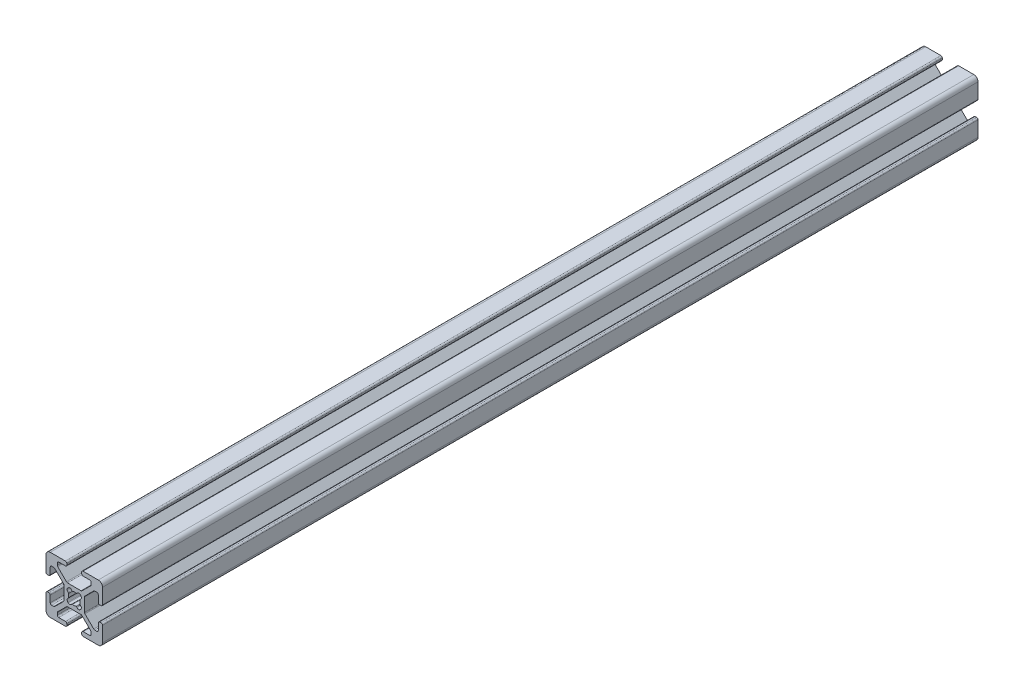
SolidWorks part; units mm, degrees
ref_plane "Front Plane" through (0, 0, 0) normal (0, 0, 1) x (1, 0, 0)
ref_plane "Top Plane" through (0, 0, 0) normal (0, 1, 0) x (1, 0, 0)
ref_plane "Right Plane" through (0, 0, 0) normal (1, 0, 0) x (0, 0, -1)
sketch "Sketch1" plane through (0, 0, 0) normal (1, 0, 0) x (0, 0, -1)
  line L0 (0, 0) -> (310, 0)
  dimension "D1" = 310
other "20_series 20-2020(1)"
ref_plane "Plane1" through (0, 0, 0) normal (0, 0, -1) x (0, 1, 0)
sketch "Sketch11" plane through (0, 0, 0) normal (0, 0, -1) x (0, 1, 0)
  line L0 (9.0094, 2.6289) -> (9.492, 2.6289)
  line L1 (8.5014, 5.4864) -> (8.5014, 3.1369)
  line L2 (10, 8.5014) -> (10, 3.1369)
  line L3 (7.2645, 5.9944) -> (7.9934, 5.9944)
  line L4 (3.1369, 10) -> (8.5014, 10)
  line L5 (3.8074, 2.7477) -> (6.9053, 5.8456)
  line L6 (2.6289, 9.0094) -> (2.6289, 9.492)
  line L7 (3.6586, -2.3885) -> (3.6586, 2.3885)
  line L8 (3.1369, 8.5014) -> (5.4864, 8.5014)
  line L9 (6.9053, -5.8456) -> (3.8074, -2.7477)
  line L10 (5.9944, 7.9934) -> (5.9944, 7.2645)
  line L11 (7.9934, -5.9944) -> (7.2645, -5.9944)
  line L12 (5.8456, 6.9053) -> (2.7477, 3.8074)
  line L13 (8.5014, -3.1369) -> (8.5014, -5.4864)
  line L14 (2.3885, 3.6586) -> (-2.3885, 3.6586)
  line L15 (9.0094, -2.6289) -> (9.492, -2.6289)
  line L16 (-2.7477, 3.8074) -> (-5.8456, 6.9053)
  line L17 (10, -3.1369) -> (10, -8.5014)
  line L18 (-5.9944, 7.2645) -> (-5.9944, 7.9934)
  line L19 (8.5014, -10) -> (3.1369, -10)
  line L20 (-5.4864, 8.5014) -> (-3.1369, 8.5014)
  line L21 (2.6289, -9.0094) -> (2.6289, -9.492)
  line L22 (-2.6289, 9.0094) -> (-2.6289, 9.492)
  line L23 (5.4864, -8.5014) -> (3.1369, -8.5014)
  line L24 (-8.5014, 10) -> (-3.1369, 10)
  line L25 (5.9944, -7.2645) -> (5.9944, -7.9934)
  line L26 (-10, 3.1369) -> (-10, 8.5014)
  line L27 (2.7477, -3.8074) -> (5.8456, -6.9053)
  line L28 (-9.0094, 2.6289) -> (-9.492, 2.6289)
  line L29 (-2.3885, -3.6586) -> (2.3885, -3.6586)
  line L30 (-8.5014, 3.1369) -> (-8.5014, 5.4864)
  line L31 (-5.8456, -6.9053) -> (-2.7477, -3.8074)
  line L32 (-7.9934, 5.9944) -> (-7.2645, 5.9944)
  line L33 (-5.9944, -7.9934) -> (-5.9944, -7.2645)
  line L34 (-6.9053, 5.8456) -> (-3.8074, 2.7477)
  line L35 (-3.1369, -8.5014) -> (-5.4864, -8.5014)
  line L36 (-3.6586, 2.3885) -> (-3.6586, -2.3885)
  line L37 (-2.6289, -9.0094) -> (-2.6289, -9.492)
  line L38 (-3.8074, -2.7477) -> (-6.9053, -5.8456)
  line L39 (-3.1369, -10) -> (-8.5014, -10)
  line L40 (-7.2645, -5.9944) -> (-7.9934, -5.9944)
  line L41 (-10, -8.5014) -> (-10, -3.1369)
  line L42 (-8.5014, -5.4864) -> (-8.5014, -3.1369)
  line L43 (-9.0094, -2.6289) -> (-9.492, -2.6289)
  line L44 (-2.2966, 2.1217) -> (-2.1217, 2.2966)
  line L45 (2.1217, 2.2966) -> (2.2966, 2.1217)
  line L46 (-2.1217, -2.2966) -> (-2.2966, -2.1217)
  line L47 (2.2966, -2.1217) -> (2.1217, -2.2966)
  arc A0 (8.5014, 3.1369) -> (9.0094, 2.6289) centre (9.0094, 3.1369) ccw
  arc A1 (9.492, 2.6289) -> (10, 3.1369) centre (9.492, 3.1369) ccw
  arc A2 (8.5014, 5.4864) -> (7.9934, 5.9944) centre (7.9934, 5.4864) ccw
  arc A3 (10, 8.5014) -> (8.5014, 10) centre (8.5014, 8.5014) ccw
  arc A4 (7.2645, 5.9944) -> (6.9053, 5.8456) centre (7.2645, 5.4864) ccw
  arc A5 (3.1369, 10) -> (2.6289, 9.492) centre (3.1369, 9.492) ccw
  arc A6 (3.8074, 2.7477) -> (3.6586, 2.3885) centre (4.1666, 2.3885) ccw
  arc A7 (2.6289, 9.0094) -> (3.1369, 8.5014) centre (3.1369, 9.0094) ccw
  arc A8 (3.6586, -2.3885) -> (3.8074, -2.7477) centre (4.1666, -2.3885) ccw
  arc A9 (5.9944, 7.9934) -> (5.4864, 8.5014) centre (5.4864, 7.9934) ccw
  arc A10 (6.9053, -5.8456) -> (7.2645, -5.9944) centre (7.2645, -5.4864) ccw
  arc A11 (5.8456, 6.9053) -> (5.9944, 7.2645) centre (5.4864, 7.2645) ccw
  arc A12 (7.9934, -5.9944) -> (8.5014, -5.4864) centre (7.9934, -5.4864) ccw
  arc A13 (2.3885, 3.6586) -> (2.7477, 3.8074) centre (2.3885, 4.1666) ccw
  arc A14 (9.0094, -2.6289) -> (8.5014, -3.1369) centre (9.0094, -3.1369) ccw
  arc A15 (-2.7477, 3.8074) -> (-2.3885, 3.6586) centre (-2.3885, 4.1666) ccw
  arc A16 (10, -3.1369) -> (9.492, -2.6289) centre (9.492, -3.1369) ccw
  arc A17 (-5.9944, 7.2645) -> (-5.8456, 6.9053) centre (-5.4864, 7.2645) ccw
  arc A18 (8.5014, -10) -> (10, -8.5014) centre (8.5014, -8.5014) ccw
  arc A19 (-5.4864, 8.5014) -> (-5.9944, 7.9934) centre (-5.4864, 7.9934) ccw
  arc A20 (2.6289, -9.492) -> (3.1369, -10) centre (3.1369, -9.492) ccw
  arc A21 (-3.1369, 8.5014) -> (-2.6289, 9.0094) centre (-3.1369, 9.0094) ccw
  arc A22 (3.1369, -8.5014) -> (2.6289, -9.0094) centre (3.1369, -9.0094) ccw
  arc A23 (-2.6289, 9.492) -> (-3.1369, 10) centre (-3.1369, 9.492) ccw
  arc A24 (5.4864, -8.5014) -> (5.9944, -7.9934) centre (5.4864, -7.9934) ccw
  arc A25 (-8.5014, 10) -> (-10, 8.5014) centre (-8.5014, 8.5014) ccw
  arc A26 (5.9944, -7.2645) -> (5.8456, -6.9053) centre (5.4864, -7.2645) ccw
  arc A27 (-10, 3.1369) -> (-9.492, 2.6289) centre (-9.492, 3.1369) ccw
  arc A28 (2.7477, -3.8074) -> (2.3885, -3.6586) centre (2.3885, -4.1666) ccw
  arc A29 (-9.0094, 2.6289) -> (-8.5014, 3.1369) centre (-9.0094, 3.1369) ccw
  arc A30 (-2.3885, -3.6586) -> (-2.7477, -3.8074) centre (-2.3885, -4.1666) ccw
  arc A31 (-7.9934, 5.9944) -> (-8.5014, 5.4864) centre (-7.9934, 5.4864) ccw
  arc A32 (-5.8456, -6.9053) -> (-5.9944, -7.2645) centre (-5.4864, -7.2645) ccw
  arc A33 (-6.9053, 5.8456) -> (-7.2645, 5.9944) centre (-7.2645, 5.4864) ccw
  arc A34 (-5.9944, -7.9934) -> (-5.4864, -8.5014) centre (-5.4864, -7.9934) ccw
  arc A35 (-3.6586, 2.3885) -> (-3.8074, 2.7477) centre (-4.1666, 2.3885) ccw
  arc A36 (-2.6289, -9.0094) -> (-3.1369, -8.5014) centre (-3.1369, -9.0094) ccw
  arc A37 (-3.8074, -2.7477) -> (-3.6586, -2.3885) centre (-4.1666, -2.3885) ccw
  arc A38 (-3.1369, -10) -> (-2.6289, -9.492) centre (-3.1369, -9.492) ccw
  arc A39 (-7.2645, -5.9944) -> (-6.9053, -5.8456) centre (-7.2645, -5.4864) ccw
  arc A40 (-10, -8.5014) -> (-8.5014, -10) centre (-8.5014, -8.5014) ccw
  arc A41 (-8.5014, -5.4864) -> (-7.9934, -5.9944) centre (-7.9934, -5.4864) ccw
  arc A42 (-9.492, -2.6289) -> (-10, -3.1369) centre (-9.492, -3.1369) ccw
  arc A43 (-8.5014, -3.1369) -> (-9.0094, -2.6289) centre (-9.0094, -3.1369) ccw
  arc A44 (-0.8806, 2.1293) -> (-0.5885, 2.0112) centre (-0.6599, 2.2549) ccw
  arc A45 (0.5885, 2.0112) -> (-0.5885, 2.0112) centre (0, 0) ccw
  arc A46 (-0.8806, 2.1293) -> (-2.1217, 2.2966) centre (-1.565, 1.7398) ccw
  arc A47 (0.5885, 2.0112) -> (0.8806, 2.1293) centre (0.6599, 2.2549) ccw
  arc A48 (2.1217, 2.2966) -> (0.8806, 2.1293) centre (1.565, 1.7398) ccw
  arc A49 (-2.2966, 2.1217) -> (-2.1293, 0.8806) centre (-1.7398, 1.565) ccw
  arc A50 (-2.0112, 0.5885) -> (-2.1293, 0.8806) centre (-2.2549, 0.6599) ccw
  arc A51 (2.1293, 0.8806) -> (2.2966, 2.1217) centre (1.7398, 1.565) ccw
  arc A52 (-2.0112, 0.5885) -> (-2.0112, -0.5885) centre (0, 0) ccw
  arc A53 (2.1293, 0.8806) -> (2.0112, 0.5885) centre (2.2549, 0.6599) ccw
  arc A54 (-2.1293, -0.8806) -> (-2.0112, -0.5885) centre (-2.2549, -0.6599) ccw
  arc A55 (2.0112, -0.5885) -> (2.0112, 0.5885) centre (0, 0) ccw
  arc A56 (-2.1293, -0.8806) -> (-2.2966, -2.1217) centre (-1.7398, -1.565) ccw
  arc A57 (2.0112, -0.5885) -> (2.1293, -0.8806) centre (2.2549, -0.6599) ccw
  arc A58 (2.2966, -2.1217) -> (2.1293, -0.8806) centre (1.7398, -1.565) ccw
  arc A59 (-2.1217, -2.2966) -> (-0.8806, -2.1293) centre (-1.565, -1.7398) ccw
  arc A60 (-0.5885, -2.0112) -> (-0.8806, -2.1293) centre (-0.6599, -2.2549) ccw
  arc A61 (0.8806, -2.1293) -> (2.1217, -2.2966) centre (1.565, -1.7398) ccw
  arc A62 (-0.5885, -2.0112) -> (0.5885, -2.0112) centre (0, 0) ccw
  arc A63 (0.8806, -2.1293) -> (0.5885, -2.0112) centre (0.6599, -2.2549) ccw
  point P0 (0, 0)
